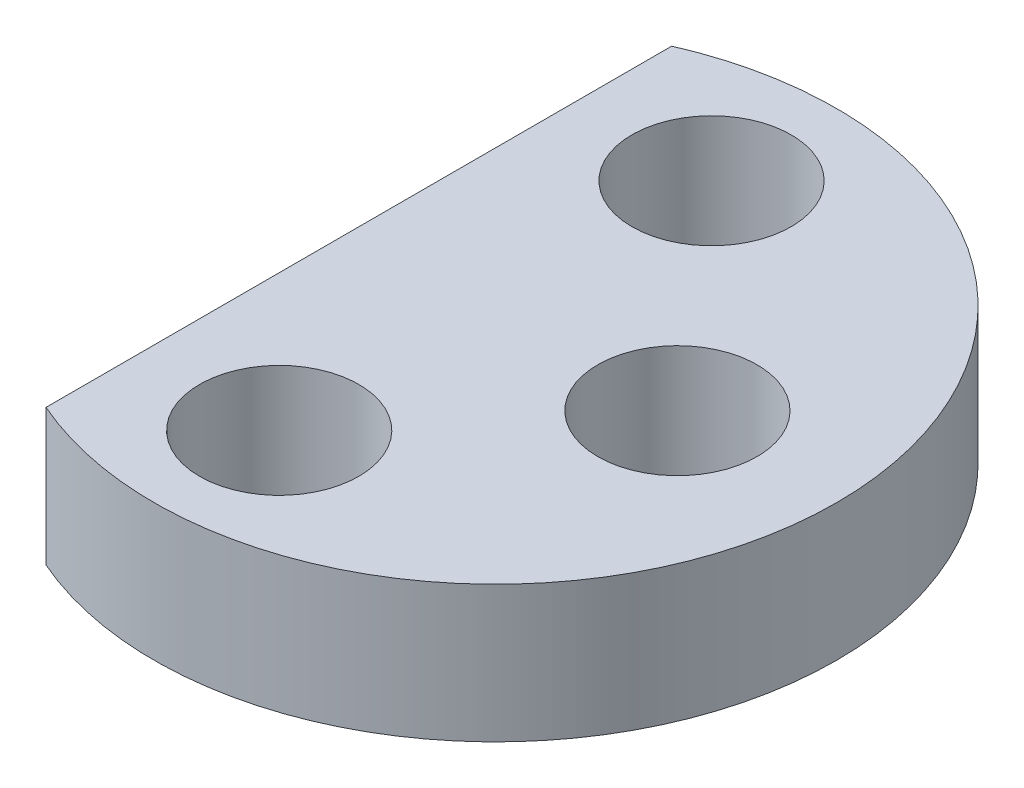
SolidWorks part; units mm, degrees
ref_plane "Front Plane" through (0, 0, 0) normal (0, 0, 1) x (1, 0, 0)
ref_plane "Top Plane" through (0, 0, 0) normal (0, 1, 0) x (1, 0, 0)
ref_plane "Right Plane" through (0, 0, 0) normal (1, 0, 0) x (0, 0, -1)
sketch "Sketch1" plane through (0, 0, 0) normal (0, 1, 0) x (1, 0, 0)
  line L0 (0, 4.75) -> (0, -4.75) construction
  line L1 (-3, 6.8739) -> (-3, -6.8739)
  arc A0 (-3, -6.8739) -> (-3, 6.8739) centre (0, 0) ccw
  circle A1 centre (0, 4.75) radius 1.75
  circle A2 centre (0, -4.75) radius 1.75
  circle A3 centre (4, 0) radius 1.75
  point P9 (0, 0)
  dimension "D1" = 3.5
  dimension "D2" = 15
  dimension "D3" = 9.5
  dimension "D4" = 4
  dimension "D5" = 3
extrude "Boss-Extrude1" add sketch "Sketch1" along normal blind 3
